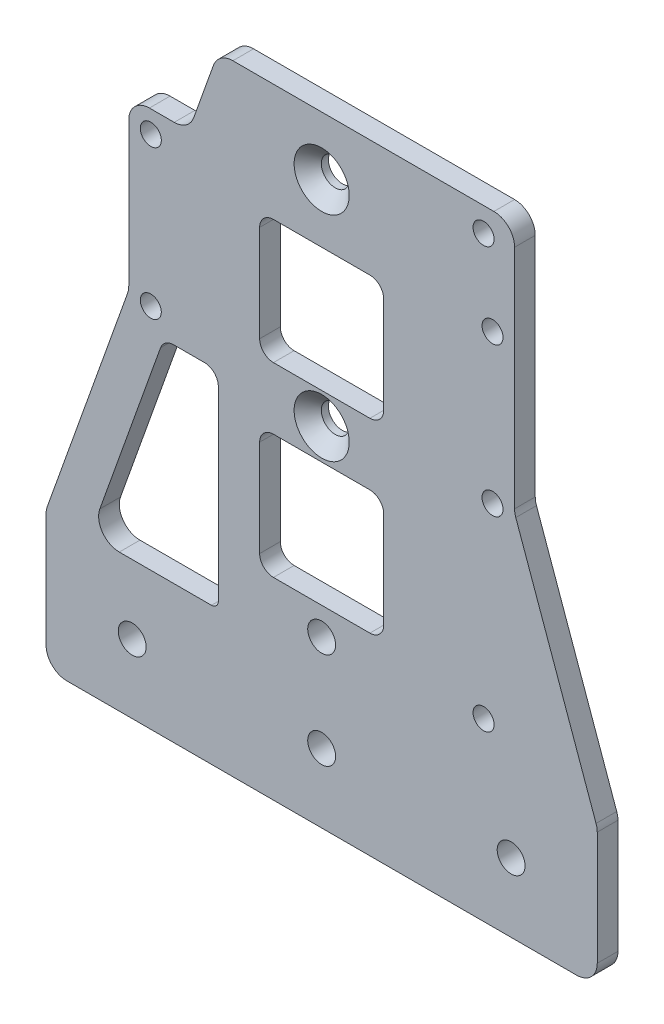
SolidWorks part; units mm, degrees
material "Thornel Mat VMA"
ref_plane "前视基准面" through (0, 0, 0) normal (0, 0, 1) x (1, 0, 0)
ref_plane "上视基准面" through (0, 0, 0) normal (0, 1, 0) x (1, 0, 0)
ref_plane "右视基准面" through (0, 0, 0) normal (1, 0, 0) x (0, 0, -1)
other "Configuration Table"
sketch "草图1" plane through (0, 0, 0) normal (0, 0, 1) x (1, 0, 0)
  line L8 (40, 0) -> (-40, 0)
  line L9 (-40, 0) -> (-40, 20)
  line L10 (-40, 20) -> (-15, 90)
  line L11 (-15, 90) -> (15, 90)
  line L12 (15, 90) -> (40, 20)
  line L13 (40, 20) -> (40, 0)
  line L14 (0, 0) -> (0, 90) construction
  dimension "D1" = 20
  dimension "D2" = 30
  dimension "D3" = 90
  dimension "D4" = 80
extrude "凸台-拉伸1" add sketch "草图1" along normal mid plane 3
sketch "草图2" plane through (0, 0, 1.5) normal (0, 0, 1) x (1, 0, 0)
  line L0 (-15, 72.1607) -> (-33.6288, 20)
  line L3 (-33.6288, 20) -> (-15, 20)
  line L10 (-15, 20) -> (-15, 72.1607)
  line L11 (-15, 90) -> (-40, 20) construction
  line L12 (-40, 0) -> (40, 0) construction
  line L13 (-40, 20) -> (-40, 0) construction
  line L14 (0, 0) -> (0, 28) construction
  line L15 (-9, 55) -> (9, 55)
  line L16 (-9, 55) -> (-9, 73)
  line L17 (-9, 73) -> (9, 73)
  line L18 (9, 55) -> (9, 73)
  line L19 (-9, 55) -> (9, 73) construction
  line L20 (-9, 73) -> (9, 55) construction
  line L21 (-9, 28) -> (9, 28)
  line L22 (-9, 28) -> (-9, 46)
  line L23 (-9, 46) -> (9, 46)
  line L24 (9, 28) -> (9, 46)
  line L25 (-9, 28) -> (9, 46) construction
  line L26 (-9, 46) -> (9, 28) construction
  line L27 (15, 20) -> (15, 72.1607) construction
  line L28 (33.6288, 20) -> (15, 20) construction
  line L29 (15, 72.1607) -> (33.6288, 20) construction
  point P2 (0, 37)
  point P11 (0, 64)
  dimension "D1" = 6
  dimension "D5" = 28
  dimension "D2" = 20
  dimension "D3" = 25
  dimension "D4" = 18
  dimension "D6" = 9
extrude "切除-拉伸1" cut sketch "草图2" against normal up to surface (3 mm away) up to face at (0, 36.6667, -1.5)
fillet "圆角1" radius 1 2 edges at (-15, 20, 0) (-15, 72.1607, 0)
fillet "圆角2" radius 2 8 edges at (9, 73, 0) (9, 55, 0) (-9, 55, 0) (-9, 73, 0) (9, 28, 0) (-9, 46, 0) (9, 46, 0) (-9, 28, 0)
fillet "圆角3" radius 3 6 edges at (40, 0, 0) (-40, 0, 0) (-40, 20, 0) (15, 90, 0) (40, 20, 0) (-15, 90, 0)
sketch "草图3" plane through (0, 0, 1.5) normal (0, 0, 1) x (1, 0, 0)
  line L0 (-37, 0) -> (37, 0) construction
  line L1 (0, 0) -> (0, 28) construction
  line L2 (-7, 28) -> (7, 28) construction
  circle A0 centre (-27.5, 10) radius 2.025
  circle A1 centre (27.5, 10) radius 2.025
  dimension "D1" = 55
  dimension "D2" = 4.05
  dimension "D3" = 10
extrude "切除-拉伸2" cut sketch "草图3" against normal through all both and the other way through all
sketch "草图4" plane through (0, 0, 1.5) normal (0, 0, 1) x (1, 0, 0)
  line L0 (-27.5, 10) -> (0, 10) construction
  circle A0 centre (0, 10) radius 2.025
  dimension "D1" = 4.05
extrude "切除-拉伸3" cut sketch "草图4" against normal through all both
sketch "草图5" plane through (0, 0, 1.5) normal (0, 0, 1) x (1, 0, 0)
  line L0 (-7, 28) -> (7, 28) construction
  line L1 (0, 55) -> (0, 46) construction
  line L2 (-7, 55) -> (7, 55) construction
  line L3 (7, 46) -> (-7, 46) construction
  line L4 (0, 73) -> (0, 90) construction
  line L5 (7, 73) -> (-7, 73) construction
  line L6 (12.8858, 90) -> (-12.8858, 90) construction
  circle A0 centre (0, 24) radius 2.025
  circle A1 centre (0, 50.5) radius 2.025
  circle A2 centre (0, 81.5) radius 2.025
  dimension "D1" = 4.05
  dimension "D2" = 4
extrude "切除-拉伸4" cut sketch "草图5" against normal through all both
fillet "圆角4" radius 3 1 edges at (-33.6288, 20, 0)
sketch "草图6" plane through (0, 0, -1.5) normal (0, 0, -1) x (-1, 0, 0)
  line L0 (28, 50) -> (-28, 50) construction
  line L1 (-28, 50) -> (28, 50)
  line L2 (-28, 50) -> (-28, 78)
  line L3 (-28, 78) -> (28, 78)
  line L4 (28, 50) -> (28, 78)
  line L5 (-28, 50) -> (28, 78) construction
  line L6 (-28, 78) -> (28, 50) construction
  line L7 (-39.8252, 20.4894) -> (-15.7111, 88.009) construction
  line L8 (15.7111, 88.009) -> (39.8252, 20.4894) construction
  line L9 (-39.8252, 20.4894) -> (-15.7111, 88.009)
  line L10 (15.7111, 88.009) -> (39.8252, 20.4894)
  line L11 (15, 21) -> (15, 66.3875) construction
  line L12 (16.9417, 66.7238) -> (32.197, 24.009) construction
  line L15 (15, 21) -> (15, 66.3875)
  line L16 (16.9417, 66.7238) -> (32.197, 24.009)
  arc A0 (16.9417, 66.7238) -> (15, 66.3875) centre (16, 66.3875) ccw construction
  arc A2 (16.9417, 66.7238) -> (15, 66.3875) centre (16, 66.3875) ccw
  point P0 (0, 64)
extrude "凸台-拉伸2" add sketch "草图6" against normal up to surface (3 mm away)
fillet "圆角5" radius 3 6 edges at (-28, 53.6, 0) (-19.2857, 78, 0) (19.2857, 78, 0) (28, 78, 0) (28, 53.6, 0) (-28, 78, 0)
sketch "草图7" plane through (0, 0, -1.5) normal (0, 0, -1) x (-1, 0, 0)
  line L0 (-12.8858, 90) -> (12.8858, 90) construction
  line L1 (-24.8, 53.2) -> (24.8, 53.2) construction
  line L2 (-24.8, 53.2) -> (-24.8, 74.8) construction
  line L3 (-24.8, 74.8) -> (24.8, 74.8) construction
  line L4 (24.8, 53.2) -> (24.8, 74.8) construction
  line L5 (-24.8, 53.2) -> (24.8, 74.8) construction
  line L6 (-24.8, 74.8) -> (24.8, 53.2) construction
  line L9 (18.9573, 50) -> (18.9573, 78) construction
  line L10 (15, 50) -> (22.9145, 50) construction
  line L11 (21.3999, 78) -> (25, 78) construction
  circle A0 centre (24.8, 74.8) radius 1.525
  circle A1 centre (24.8, 53.2) radius 1.525
  circle A2 centre (-24.8, 53.2) radius 1.525
  circle A3 centre (-24.8, 74.8) radius 1.525
  point P0 (0, 64)
  point P7 (0, 90)
  point P8 (0, 74.8)
  point P16 (18.9573, 64)
  dimension "D3" = 3.05
  dimension "D1" = 21.6
  dimension "D2" = 49.6
extrude "切除-拉伸5" cut sketch "草图7" against normal up to surface (3 mm away) up to face at (0, 53.2667, 1.5)
hole_wizard "孔1" positions "草图8" profile "草图9" legacy
sketch "草图8" plane through (0, 0, 1.5) normal (0, 0, 1) x (1, 0, 0)
  point P0 (0, 81.5)
  point P3 (0, 50.5)
sketch "草图9" plane through (0, 81.5, 1.5) normal (1, 0, 0) x (0, -1, 0)
  line L0 (0, 0) -> (0, 100)
  line L1 (0, 100) -> (2.025, 100)
  line L2 (2.025, 100) -> (2.025, 1.975)
  line L3 (2.025, 1.975) -> (4, 0)
  line L4 (4, 0) -> (0, 0)
  line L5 (0, -6.4453) -> (0, 115.525) construction
  line L6 (-2.025, 1.975) -> (-4, 0) construction
  dimension "直径" = 4.05
  dimension "深度" = 100
  dimension "锥坑角度" = 90
  dimension "锥坑直径" = 8
sketch "草图11" plane through (0, 0, 1.5) normal (0, 0, 1) x (1, 0, 0)
  line L0 (12.8858, 90) -> (28, 90)
  line L1 (28, 90) -> (28, 75)
  line L2 (25, 78) -> (21.3999, 78) construction
  line L3 (18.5746, 79.991) -> (15.7111, 88.009) construction
  line L4 (25, 78) -> (21.3999, 78)
  line L5 (18.5746, 79.991) -> (15.7111, 88.009)
  arc A0 (28, 75) -> (25, 78) centre (25, 75) ccw construction
  arc A1 (18.5746, 79.991) -> (21.3999, 78) centre (21.3999, 81) ccw construction
  arc A2 (15.7111, 88.009) -> (12.8858, 90) centre (12.8858, 87) ccw construction
  arc A3 (28, 75) -> (25, 78) centre (25, 75) ccw
  arc A4 (18.5746, 79.991) -> (21.3999, 78) centre (21.3999, 81) ccw
  arc A5 (15.7111, 88.009) -> (12.8858, 90) centre (12.8858, 87) ccw
extrude "凸台-拉伸3" add sketch "草图11" against normal up to surface (3 mm away)
fillet "圆角6" radius 3 1 edges at (28, 90, 0)
sketch "草图12" plane through (0, 0, 1.5) normal (0, 0, 1) x (1, 0, 0)
  circle A0 centre (23.5, 86.5) radius 1.525
  circle A2 centre (23.5, 25.5) radius 1.525
  circle A3 centre (23.5, 86.5) radius 1.525 construction
  circle A5 centre (23.5, 25.5) radius 1.525 construction
  dimension "D1" = 3.05
extrude "切除-拉伸6" cut sketch "草图12" against normal through all both and the other way through all
fillet "圆角7" radius 2 2 edges at (-15, 50, 0) (-22.9145, 50, 0)
